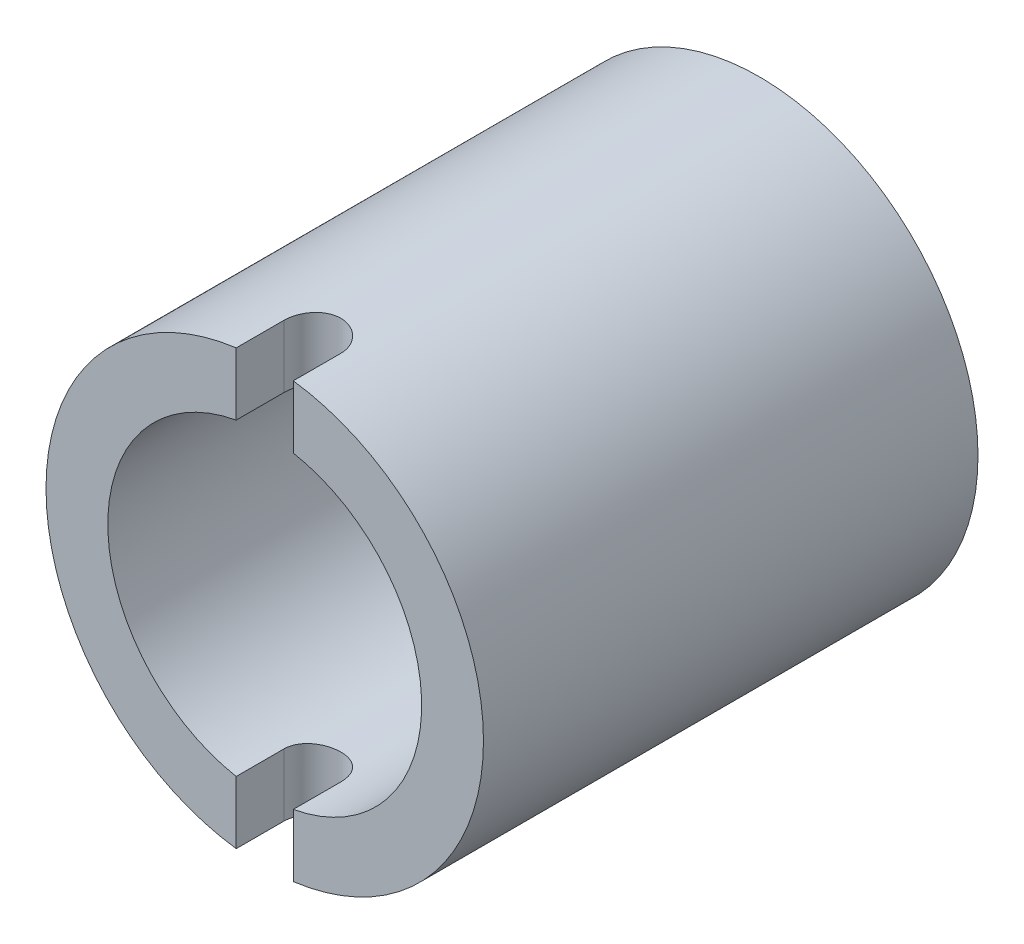
SolidWorks part; units mm, degrees
ref_plane "Front Plane" through (0, 0, 0) normal (0, 0, 1) x (1, 0, 0)
ref_plane "Top Plane" through (0, 0, 0) normal (0, 1, 0) x (1, 0, 0)
ref_plane "Right Plane" through (0, 0, 0) normal (1, 0, 0) x (0, 0, -1)
sketch "Sketch1" plane through (0, 0, 0) normal (0, 0, 1) x (1, 0, 0)
  circle A0 centre (0, 0) radius 9.1281
  circle A1 centre (0, 0) radius 6.5484
  dimension "D1" = 18.2562
  dimension "D2" = 13.0969
extrude "Extrude1" add sketch "Sketch1" along normal blind 20.6375
sketch "Sketch2" plane through (0, 0, 0) normal (0, 1, 0) x (1, 0, 0)
  line L0 (0, 0) -> (0, -20.6375) construction
  line L1 (-9.1281, -20.6375) -> (9.1281, -20.6375) construction
  line L2 (-1.1906, -20.6375) -> (-1.1906, -18.6531)
  line L3 (1.1906, -18.6531) -> (1.1906, -20.6375)
  line L4 (1.1906, -20.6375) -> (-1.1906, -20.6375)
  arc A0 (-1.1906, -18.6531) -> (1.1906, -18.6531) centre (0, -18.6531) cw
  dimension "D1" = 2.3813
  dimension "D2" = 3.175
extrude "Cut-Extrude1" cut sketch "Sketch2" against normal through all and the other way through all
